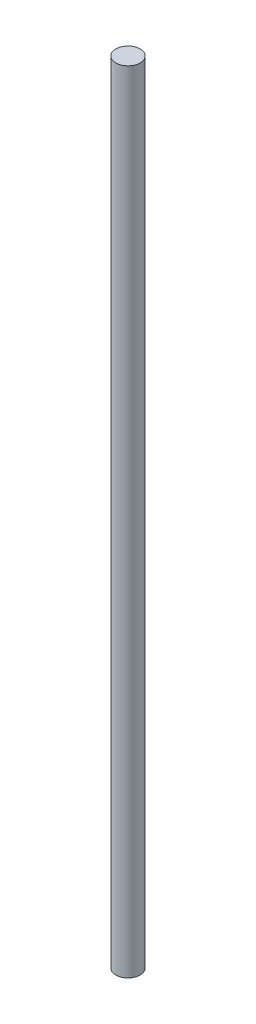
SolidWorks part; units mm, degrees
ref_plane "Front Plane" through (0, 0, 0) normal (0, 0, 1) x (1, 0, 0)
ref_plane "Top Plane" through (0, 0, 0) normal (0, 1, 0) x (1, 0, 0)
ref_plane "Right Plane" through (0, 0, 0) normal (1, 0, 0) x (0, 0, -1)
sketch "Sketch1" plane through (0, 0, 0) normal (0, 1, 0) x (1, 0, 0)
  circle A0 centre (0, 0) radius 4
  dimension "D1" = 8
extrude "Boss-Extrude1" add sketch "Sketch1" along normal blind 260
